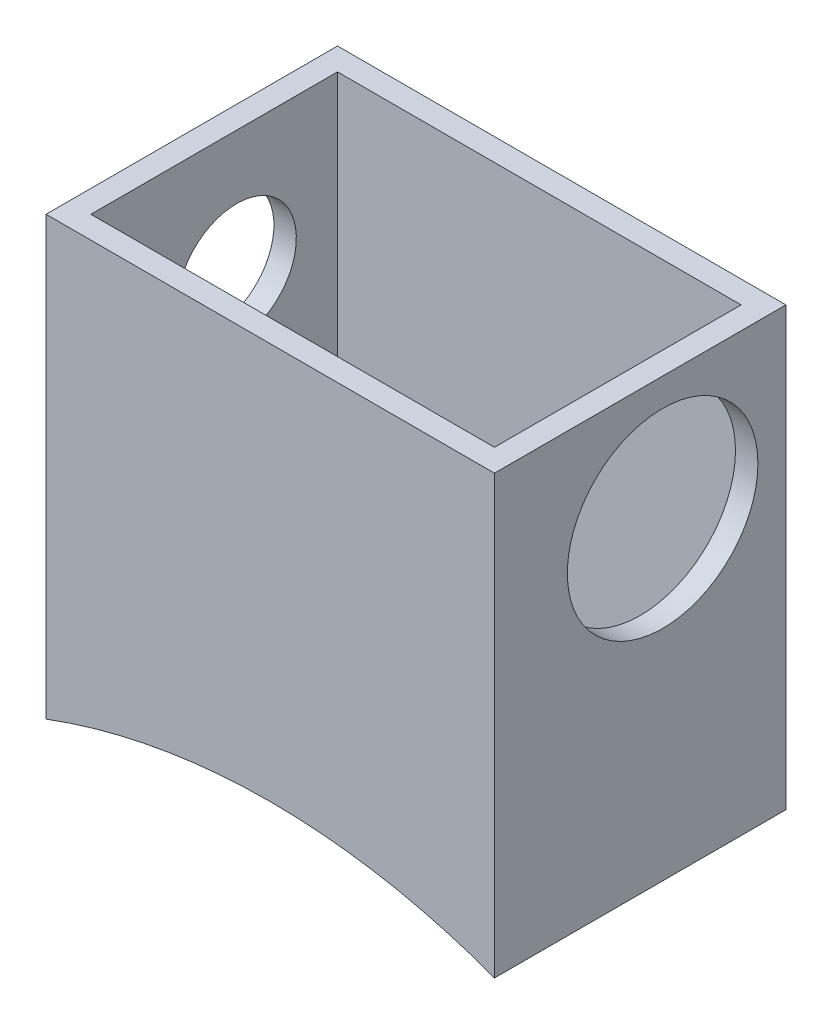
SolidWorks part; units mm, degrees
ref_plane "Front Plane" through (0, 0, 0) normal (0, 0, 1) x (1, 0, 0)
ref_plane "Top Plane" through (0, 0, 0) normal (0, 1, 0) x (1, 0, 0)
ref_plane "Right Plane" through (0, 0, 0) normal (1, 0, 0) x (0, 0, -1)
sketch "Sketch1" plane through (0, 0, 0) normal (0, 0, 1) x (1, 0, 0)
  line L0 (-3.3539, 7.6347) -> (-3.3539, -2.2713)
  line L1 (-3.3539, -2.2713) -> (6.8061, -2.2713)
  line L2 (6.8061, -2.2713) -> (6.8061, 7.6347)
  line L3 (6.2981, 7.6347) -> (6.2981, -0.7473)
  line L4 (6.2981, -0.7473) -> (-2.8459, -0.7473)
  line L5 (-2.8459, -0.7473) -> (-2.8459, 7.6347)
  line L6 (-2.8459, 7.6347) -> (-3.3539, 7.6347)
  line L7 (6.2981, 7.6347) -> (6.8061, 7.6347)
  dimension "D1" = 0.508
  dimension "D2" = 10.16
  dimension "D3" = 0.508
  dimension "D4" = 8.382
  dimension "D5" = 9.906
  dimension "D6" = 8.382
extrude "Boss-Extrude1" add sketch "Sketch1" along normal blind 5.588
sketch "Sketch2" plane through (-3.3539, 0, 0) normal (-1, 0, 0) x (0, 0, 1)
  line L0 (5.588, 7.6347) -> (0, 7.6347) construction
  line L1 (2.794, -2.2713) -> (2.794, 7.6347) construction
  point P0 (2.794, 4.8407)
  dimension "D1" = 2.794
hole_wizard "#6-32 Tapped Hole1" positions "Sketch3" profile "Sketch4" tap size "#6-32" standard "ANSI Inch" end condition up to next
sketch "Sketch3" plane through (-3.3539, 0, 0) normal (-1, 0, 0) x (0, 0, 1)
  point P0 (2.794, 4.8407)
sketch "Sketch4" plane through (-3.3539, 4.8407, 2.794) normal (0, 1, 0) x (0, 0, 1)
  line L0 (0, 0) -> (0, 0.508)
  line L1 (0, 0.508) -> (1.3525, 0.508)
  line L2 (1.3525, 0.508) -> (1.3525, 0)
  line L5 (1.3525, 0) -> (0, 0)
  line L11 (0, -6.35) -> (0, 107.95) construction
  dimension "Thread Major Dia." = 2.7051
  dimension "Thru Tap Drill Depth" = 0.508
sketch "Sketch5" plane through (6.8061, 0, 0) normal (1, 0, 0) x (0, 0, -1)
  point P0 (-2.794, 4.8407)
sketch "Sketch6" plane through (6.8061, 0, 0) normal (1, 0, 0) x (0, 0, -1)
  circle A0 centre (-2.794, 4.8407) radius 2.159
extrude "Cut-Extrude1" cut sketch "Sketch6" against normal up to next
sketch "Sketch12" plane through (-3.3539, 0, 0) normal (-1, 0, 0) x (0, 0, 1)
  line L0 (2.794, -2.2713) -> (2.794, 7.6347) construction
  line L1 (5.588, -2.2713) -> (0, -2.2713) construction
  line L2 (5.588, 7.6347) -> (0, 7.6347) construction
sketch "Sketch16" plane through (0, 0, 0) normal (0, 0, -1) x (-1, 0, 0)
  line L0 (-6.8061, -2.2713) -> (-1.7261, -15.8288) construction
  line L1 (-1.7261, -15.8288) -> (3.3539, -2.2713) construction
  line L2 (3.3539, -2.2713) -> (-6.8061, -2.2713)
  arc A0 (-6.8061, -2.2713) -> (3.3539, -2.2713) centre (-1.7261, -15.8288) cw
  dimension "D1" = 14.478
  dimension "D2" = 14.478
extrude "Cut-Extrude2" cut sketch "Sketch16" against normal through all
sketch "Sketch19" plane through (0, 0, 5.588) normal (0, 0, 1) x (1, 0, 0)
  line L0 (6.8061, -2.2713) -> (6.8061, 7.6347) construction
  line L1 (6.8061, 7.6347) -> (6.2981, 7.6347)
  line L5 (-2.8459, 7.6347) -> (-3.3539, 7.6347)
  line L6 (-3.3539, 7.6347) -> (-3.3539, -2.2713)
  line L7 (6.8061, -2.2713) -> (6.8061, 7.6347)
  line L8 (6.2981, 7.6347) -> (-2.8459, 7.6347)
  arc A0 (-3.3539, -2.2713) -> (6.8061, -2.2713) centre (1.7261, -15.8288) cw
extrude "Boss-Extrude3" add sketch "Sketch19" along normal blind 1.016
sketch "Sketch20" plane through (0, 7.6347, 0) normal (0, 1, 0) x (1, 0, 0)
  line L0 (-2.8459, -5.588) -> (-2.8459, -8.1549)
  line L1 (-2.8459, -5.588) -> (6.2981, -5.588)
  line L2 (6.2981, -5.588) -> (6.2981, -8.1549)
  line L3 (6.2981, -8.1549) -> (-2.8459, -8.1549)
extrude "Cut-Extrude3" cut sketch "Sketch20" against normal blind 8.382
sketch "Sketch22" plane through (0, 0, 6.604) normal (0, 0, 1) x (1, 0, 0)
  line L0 (-2.8459, 7.6347) -> (-2.8459, -0.7473)
  line L1 (-2.8459, -0.7473) -> (6.2981, -0.7473)
  line L2 (6.2981, -0.7473) -> (6.2981, 7.6347)
  line L3 (6.2981, 7.6347) -> (-2.8459, 7.6347)
extrude "Boss-Extrude4" add sketch "Sketch22" against normal blind 0.508
sketch "Sketch24" plane through (0, 0, 0) normal (0, 0, -1) x (-1, 0, 0)
  line L0 (2.8459, -0.7473) -> (2.8459, 7.6347)
  line L1 (2.8459, 7.6347) -> (-6.2981, 7.6347)
  line L2 (-6.2981, 7.6347) -> (-6.2981, -0.7473)
  line L3 (-6.2981, -0.7473) -> (2.8459, -0.7473)
extrude "Boss-Extrude5" add sketch "Sketch24" against normal blind 0.508
ref_plane "Plane2" through (0, 0, 3.302) normal (0, 0, -1) x (-1, 0, 0)
ref_plane "Plane5" through (1.7261, 0, 0) normal (-1, 0, 0) x (0, 0, 1)
